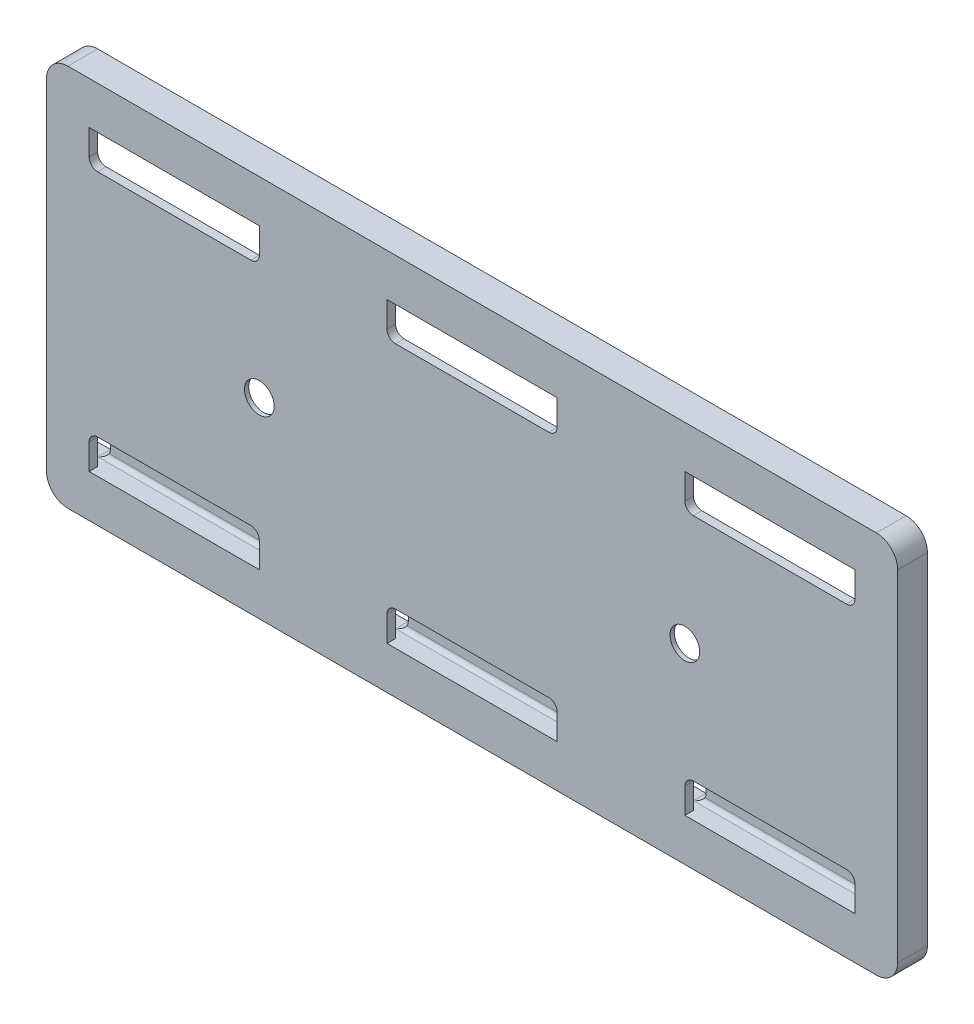
SolidWorks part; units mm, degrees
ref_plane "Plano frontal" through (0, 0, 0) normal (0, 0, 1) x (1, 0, 0)
ref_plane "Plano superior" through (0, 0, 0) normal (0, 1, 0) x (1, 0, 0)
ref_plane "Plano direito" through (0, 0, 0) normal (1, 0, 0) x (0, 0, -1)
sketch "Esboço1" plane through (0, 0, 0) normal (0, 0, 1) x (1, 0, 0)
  line L1 (-50, -22.5) -> (50, -22.5)
  line L2 (-50, -22.5) -> (-50, 22.5)
  line L3 (-50, 22.5) -> (50, 22.5)
  line L4 (50, -22.5) -> (50, 22.5)
  line L5 (-50, -22.5) -> (50, 22.5) construction
  line L6 (-50, 22.5) -> (50, -22.5) construction
  point P0 (0, 0)
  dimension "D1" = 45
  dimension "D2" = 100
extrude "Ressalto-extrusão1" add sketch "Esboço1" along normal blind 3.5
sketch "Esboço2" plane through (0, 0, 0) normal (0, 0, -1) x (-1, 0, 0)
  line L0 (-51.8558, 0) -> (52.4553, 0) construction
  line L1 (0.2997, 26.0278) -> (0.2997, -25.3284) construction
  line L2 (50, 22.5) -> (50, -22.5) construction
  line L3 (50, 17.5) -> (-47.5, 17.5)
  line L4 (50, 17.5) -> (50, -17.5)
  line L5 (50, -17.5) -> (-47.5, -17.5)
  line L6 (-47.5, 17.5) -> (-47.5, -17.5)
  line L7 (50, -22.5) -> (-50, -22.5) construction
  line L8 (-50, -22.5) -> (-50, 22.5) construction
  dimension "D1" = 35
  dimension "D2" = 5
  dimension "D3" = 2.5
extrude "Corte-extrusão1" cut sketch "Esboço2" against normal blind 2.5
sketch "Esboço4" plane through (0, 0, 0) normal (0, 0, -1) x (-1, 0, 0)
  line L0 (50, -22.5) -> (-50, -22.5) construction
  line L1 (-45, -22.5) -> (-25, -22.5)
  line L2 (-45, -22.5) -> (-45, -15.5)
  line L3 (-44, -14.5) -> (-26, -14.5)
  line L4 (-25, -22.5) -> (-25, -15.5)
  line L5 (50, -17.5) -> (50, 17.5) construction
  line L6 (-47.5, 17.5) -> (-47.5, -17.5) construction
  line L7 (0, 0) -> (-58.2504, 0) construction
  line L8 (-47.5, -17.5) -> (50, -17.5) construction
  line L10 (-10, -22.5) -> (10, -22.5)
  line L11 (-10, -22.5) -> (-10, -15.5)
  line L12 (-9, -14.5) -> (9, -14.5)
  line L13 (10, -22.5) -> (10, -15.5)
  line L14 (25, -22.5) -> (45, -22.5)
  line L15 (25, -22.5) -> (25, -15.5)
  line L16 (26, -14.5) -> (44, -14.5)
  line L17 (45, -22.5) -> (45, -15.5)
  line L19 (26, 14.5) -> (44, 14.5)
  line L20 (45, 22.5) -> (45, 15.5)
  line L21 (25, 22.5) -> (45, 22.5)
  line L22 (25, 22.5) -> (25, 15.5)
  line L23 (-9, 14.5) -> (9, 14.5)
  line L24 (10, 22.5) -> (10, 15.5)
  line L25 (-10, 22.5) -> (10, 22.5)
  line L26 (-10, 22.5) -> (-10, 15.5)
  line L27 (-44, 14.5) -> (-26, 14.5)
  line L28 (-25, 22.5) -> (-25, 15.5)
  line L29 (-45, 22.5) -> (-25, 22.5)
  line L30 (-45, 22.5) -> (-45, 15.5)
  arc A0 (-45, -15.5) -> (-44, -14.5) centre (-44, -15.5) cw
  arc A1 (-26, -14.5) -> (-25, -15.5) centre (-26, -15.5) cw
  arc A2 (-10, -15.5) -> (-9, -14.5) centre (-9, -15.5) cw
  arc A3 (9, -14.5) -> (10, -15.5) centre (9, -15.5) cw
  arc A4 (44, -14.5) -> (45, -15.5) centre (44, -15.5) cw
  arc A5 (25, -15.5) -> (26, -14.5) centre (26, -15.5) cw
  arc A6 (-44, 14.5) -> (-45, 15.5) centre (-44, 15.5) cw
  arc A7 (-26, 14.5) -> (-25, 15.5) centre (-26, 15.5) ccw
  arc A8 (-9, 14.5) -> (-10, 15.5) centre (-9, 15.5) cw
  arc A9 (9, 14.5) -> (10, 15.5) centre (9, 15.5) ccw
  arc A10 (26, 14.5) -> (25, 15.5) centre (26, 15.5) cw
  arc A11 (44, 14.5) -> (45, 15.5) centre (44, 15.5) ccw
  point P37 (-45, -14.5)
  point P40 (-25, -14.5)
  point P43 (-10, -14.5)
  point P46 (10, -14.5)
  point P49 (45, -14.5)
  point P52 (25, -14.5)
  point P55 (-45, 14.5)
  point P58 (-25, 14.5)
  point P61 (-10, 14.5)
  point P64 (10, 14.5)
  point P67 (25, 14.5)
  point P70 (45, 14.5)
  dimension "D10" = 1
  dimension "D11" = 1
  dimension "D12" = 1
  dimension "D13" = 1
  dimension "D14" = 1
  dimension "D15" = 1
  dimension "D16" = 1
  dimension "D17" = 1
  dimension "D18" = 1
  dimension "D19" = 1
  dimension "D20" = 1
  dimension "D1" = 20
  dimension "D2" = 8
  dimension "D3" = 2.5
  dimension "D4" = 20
  dimension "D5" = 20
  dimension "D6" = 5
  dimension "D7" = 8
  dimension "D8" = 8
  dimension "D9" = 15
extrude "Ressalto-extrusão2" add sketch "Esboço4" against normal blind 1
ref_plane "Plano1" through (0, 0, 3.5) normal (0, 0, 1) x (1, 0, 0)
sketch "Esboço5" plane through (0, 0, 3.5) normal (0, 0, 1) x (1, 0, 0)
  line L0 (0, 27.6414) -> (0, -29.0702) construction
  line L1 (57.481, 0) -> (-60.6683, 0) construction
  circle A0 centre (25, 0) radius 1.75
  circle A1 centre (-25, 0) radius 1.75
  dimension "D1" = 3.5
  dimension "D2" = 25
extrude "Corte-extrusão2" cut sketch "Esboço5" against normal blind 1.5
sketch "Esboço6" plane through (0, 0, 0) normal (0, 0, 1) x (1, 0, 0)
  line L1 (46.5, -18.5) -> (23.5, -18.5)
  line L2 (47.5, -19.5) -> (47.5, -20.5)
  line L3 (46.5, -21.5) -> (23.5, -21.5)
  line L4 (22.5, -19.5) -> (22.5, -20.5)
  line L5 (20.5, -18.5) -> (-21.5, -18.5)
  line L6 (21.5, -19.5) -> (21.5, -20.5)
  line L7 (20.5, -21.5) -> (-21.5, -21.5)
  line L8 (-22.5, -19.5) -> (-22.5, -20.5)
  line L9 (-24.5, -18.5) -> (-47.5, -18.5)
  line L10 (-23.5, -19.5) -> (-23.5, -20.5)
  line L11 (-24.5, -21.5) -> (-47.5, -21.5)
  line L12 (-48.5, -19.5) -> (-48.5, -20.5)
  line L13 (-50, -22.5) -> (50, -22.5) construction
  line L14 (47.5, 17.5) -> (47.5, -17.5) construction
  line L15 (-50, -17.5) -> (-50, -22.5) construction
  line L16 (57.4926, 0) -> (-59.95, 0) construction
  line L17 (-24.5, 21.5) -> (-47.5, 21.5)
  line L18 (-48.5, 19.5) -> (-48.5, 20.5)
  line L19 (-24.5, 18.5) -> (-47.5, 18.5)
  line L20 (-23.5, 19.5) -> (-23.5, 20.5)
  line L21 (20.5, 21.5) -> (-21.5, 21.5)
  line L22 (-22.5, 19.5) -> (-22.5, 20.5)
  line L23 (20.5, 18.5) -> (-21.5, 18.5)
  line L24 (21.5, 19.5) -> (21.5, 20.5)
  line L25 (46.5, 21.5) -> (23.5, 21.5)
  line L26 (22.5, 19.5) -> (22.5, 20.5)
  line L27 (46.5, 18.5) -> (23.5, 18.5)
  line L28 (47.5, 19.5) -> (47.5, 20.5)
  arc A0 (23.5, -21.5) -> (22.5, -20.5) centre (23.5, -20.5) cw
  arc A1 (23.5, -18.5) -> (22.5, -19.5) centre (23.5, -19.5) ccw
  arc A2 (47.5, -20.5) -> (46.5, -21.5) centre (46.5, -20.5) cw
  arc A3 (46.5, -18.5) -> (47.5, -19.5) centre (46.5, -19.5) cw
  arc A4 (-21.5, -21.5) -> (-22.5, -20.5) centre (-21.5, -20.5) cw
  arc A5 (-21.5, -18.5) -> (-22.5, -19.5) centre (-21.5, -19.5) ccw
  arc A6 (21.5, -20.5) -> (20.5, -21.5) centre (20.5, -20.5) cw
  arc A7 (20.5, -18.5) -> (21.5, -19.5) centre (20.5, -19.5) cw
  arc A8 (-47.5, -21.5) -> (-48.5, -20.5) centre (-47.5, -20.5) cw
  arc A9 (-47.5, -18.5) -> (-48.5, -19.5) centre (-47.5, -19.5) ccw
  arc A10 (-23.5, -20.5) -> (-24.5, -21.5) centre (-24.5, -20.5) cw
  arc A11 (-24.5, -18.5) -> (-23.5, -19.5) centre (-24.5, -19.5) cw
  arc A12 (-47.5, 21.5) -> (-48.5, 20.5) centre (-47.5, 20.5) ccw
  arc A13 (-47.5, 18.5) -> (-48.5, 19.5) centre (-47.5, 19.5) cw
  arc A14 (-23.5, 20.5) -> (-24.5, 21.5) centre (-24.5, 20.5) ccw
  arc A15 (-24.5, 18.5) -> (-23.5, 19.5) centre (-24.5, 19.5) ccw
  arc A16 (-21.5, 21.5) -> (-22.5, 20.5) centre (-21.5, 20.5) ccw
  arc A17 (-21.5, 18.5) -> (-22.5, 19.5) centre (-21.5, 19.5) cw
  arc A18 (21.5, 20.5) -> (20.5, 21.5) centre (20.5, 20.5) ccw
  arc A19 (20.5, 18.5) -> (21.5, 19.5) centre (20.5, 19.5) ccw
  arc A20 (23.5, 21.5) -> (22.5, 20.5) centre (23.5, 20.5) ccw
  arc A21 (23.5, 18.5) -> (22.5, 19.5) centre (23.5, 19.5) cw
  arc A22 (47.5, 20.5) -> (46.5, 21.5) centre (46.5, 20.5) ccw
  arc A23 (46.5, 18.5) -> (47.5, 19.5) centre (46.5, 19.5) ccw
  point P18 (22.5, -20)
  point P21 (22.5, -21.5)
  point P26 (47.5, -21.5)
  point P29 (47.5, -18.5)
  point P32 (-22.5, -21.5)
  point P37 (21.5, -21.5)
  point P40 (21.5, -18.5)
  point P43 (-48.5, -21.5)
  point P48 (-23.5, -21.5)
  point P51 (-23.5, -18.5)
  point P54 (-1.2287, 0)
  dimension "D10" = 1
  dimension "D13" = 1
  dimension "D14" = 1
  dimension "D1" = 3
  dimension "D2" = 1
  dimension "D3" = 3
  dimension "D4" = 3
  dimension "D5" = 1.5
  dimension "D6" = 25
  dimension "D7" = 25
  dimension "D8" = 44
  dimension "D9" = 1
  dimension "D11" = 1
  dimension "D12" = 1
extrude "Corte-extrusão4" cut sketch "Esboço6" along normal blind 2.5 contours L25 A20 L26 A21 L27 A23 L28 A22 | L21 A16 L22 A17 L23 A19 L24 A18 | L17 A12 L18 A13 L19 A15 L20 A14 | A11 L9 A9 L12 A8 L11 A10 L10 | L6 A6 L7 A4 L8 A5 L5 A7 | L2 A2 L3 A0 L4 A1 L1 A3
sketch "Esboço7" plane through (0, 0, 2.5) normal (0, 0, -1) x (-1, 0, 0)
  circle A0 centre (-25, 0) radius 3.5
  circle A1 centre (25, 0) radius 3.5
  dimension "D1" = 7
extrude "Corte-extrusão6" cut sketch "Esboço7" against normal blind 0.5
sketch "Esboço8" plane through (0, 0, 2.5) normal (0, 0, -1) x (-1, 0, 0)
  line L0 (-47.5, 17.5) -> (-47.5, -17.5) construction
  line L1 (-47.5, -7.5) -> (-46.2996, -7.5)
  line L2 (-47.5, -7.5) -> (-47.5, -12.5)
  line L3 (-47.5, -12.5) -> (-46.2996, -12.5)
  line L4 (-46.2996, -7.5) -> (-46.2996, -12.5)
  line L5 (-47.5, -17.5) -> (-45, -17.5) construction
  line L6 (-47.5, 2.5) -> (-46.5, 2.5)
  line L7 (-47.5, 2.5) -> (-47.5, -2.5)
  line L8 (-47.5, -2.5) -> (-46.5, -2.5)
  line L9 (-46.5, 2.5) -> (-46.5, -2.5)
  line L10 (-47.5, 12.5) -> (-46.5, 12.5)
  line L11 (-47.5, 12.5) -> (-47.5, 7.5)
  line L12 (-47.5, 7.5) -> (-46.5, 7.5)
  line L13 (-46.5, 12.5) -> (-46.5, 7.5)
  line L14 (50, 17.5) -> (-47.5, 17.5) construction
  dimension "D1" = 5
  dimension "D2" = 5
  dimension "D3" = 5
  dimension "D4" = 5
  dimension "D5" = 5
  dimension "D6" = 5
  dimension "D7" = 1
extrude "Ressalto-extrusão3" add sketch "Esboço8" along normal blind 1
fillet "Filete1" radius 2.5 1 edges at (-50, -22.5, 1.75)
fillet "Filete2" radius 2.5 1 edges at (50, -22.5, 1.75)
fillet "Filete3" radius 2.5 1 edges at (50, 22.5, 1.75)
fillet "Filete4" radius 2.5 1 edges at (-50, 22.5, 1.75)
fillet "Filete5" radius 0.5 1 edges at (46.2996, -12.5, 2)
fillet "Filete6" radius 0.5 1 edges at (46.2996, -7.5, 2)
fillet "Filete7" radius 0.5 1 edges at (46.5, -2.5, 2)
fillet "Filete8" radius 0.5 1 edges at (46.5, 2.5, 2)
fillet "Filete9" radius 0.5 1 edges at (46.5, 7.5, 2)
fillet "Filete10" radius 0.5 1 edges at (46.5, 12.5, 2)
fillet "Filete11" radius 1 1 edges at (45, 17.5, 0.5)
fillet "Filete12" radius 1 1 edges at (47.5, 17.5, 1.25)
fillet "Filete13" radius 1 1 edges at (25, 17.5, 0.5)
fillet "Filete14" radius 1 1 edges at (10, 17.5, 0.5)
fillet "Filete15" radius 1 1 edges at (-10, 17.5, 0.5)
fillet "Filete16" radius 1 1 edges at (-25, 17.5, 0.5)
fillet "Filete17" radius 1 1 edges at (-45, 17.5, 0.5)
fillet "Filete18" radius 0.5 1 edges at (-50, 17.5, 1.25)
fillet "Filete19" radius 0.5 1 edges at (-50, -17.5, 1.25)
fillet "Filete20" radius 1 1 edges at (-45, -17.5, 0.5)
fillet "Filete21" radius 1 1 edges at (-25, -17.5, 0.5)
fillet "Filete22" radius 1 1 edges at (-10, -17.5, 0.5)
fillet "Filete23" radius 1 1 edges at (10, -17.5, 0.5)
fillet "Filete24" radius 1 1 edges at (25, -17.5, 0.5)
fillet "Filete25" radius 1 1 edges at (45, -17.5, 0.5)
fillet "Filete26" radius 1 1 edges at (47.5, -17.5, 1.25)
fillet "Filete27" radius 0.5 1 edges at (35, -17.5, 1)
fillet "Filete28" radius 0.5 1 edges at (0, -17.5, 1)
fillet "Filete29" radius 0.5 1 edges at (-35, -17.5, 1)
fillet "Filete30" radius 0.5 1 edges at (-35, 17.5, 1)
fillet "Filete31" radius 0.5 1 edges at (0, 17.5, 1)
fillet "Filete32" radius 0.5 1 edges at (35, 17.5, 1)
sketch "Esboço9" plane through (0, 0, 2.5) normal (0, 0, -1) x (-1, 0, 0)
  line L0 (25, 16.5) -> (25, 15.5) construction
  line L1 (-45, 17.5) -> (-24.9988, 17.5)
  line L2 (-45, 17.5) -> (-45, 14.5)
  line L3 (-44, 13.5) -> (-25.9988, 13.5)
  line L4 (-24.9988, 17.5) -> (-24.9988, 14.5)
  line L5 (-10, 17.5) -> (10, 17.5)
  line L6 (-47.5, 16.5) -> (-47.5, 12.5) construction
  line L7 (-47.5, 22.5) -> (47.5, 22.5) construction
  line L8 (-10, 17.5) -> (-10, 14.5)
  line L9 (-9, 13.5) -> (9, 13.5)
  line L10 (10, 17.5) -> (10, 14.5)
  line L11 (25, 17.5) -> (45, 17.5)
  line L12 (25, 17.5) -> (25, 14.5)
  line L13 (26, 13.5) -> (44, 13.5)
  line L14 (45, 17.5) -> (45, 14.5)
  line L15 (0, 0) -> (-3.3797, 0) construction
  line L16 (26, -13.5) -> (44, -13.5)
  line L17 (45, -17.5) -> (45, -14.5)
  line L18 (25, -17.5) -> (45, -17.5)
  line L19 (25, -17.5) -> (25, -14.5)
  line L20 (-9, -13.5) -> (9, -13.5)
  line L21 (10, -17.5) -> (10, -14.5)
  line L22 (-10, -17.5) -> (10, -17.5)
  line L23 (-10, -17.5) -> (-10, -14.5)
  line L24 (-44, -13.5) -> (-25.9988, -13.5)
  line L25 (-24.9988, -17.5) -> (-24.9988, -14.5)
  line L26 (-45, -17.5) -> (-24.9988, -17.5)
  line L27 (-45, -17.5) -> (-45, -14.5)
  arc A0 (44, 13.5) -> (45, 14.5) centre (44, 14.5) ccw
  arc A1 (25, 14.5) -> (26, 13.5) centre (26, 14.5) ccw
  arc A2 (9, 13.5) -> (10, 14.5) centre (9, 14.5) ccw
  arc A3 (-10, 14.5) -> (-9, 13.5) centre (-9, 14.5) ccw
  arc A4 (-25.9988, 13.5) -> (-24.9988, 14.5) centre (-25.9988, 14.5) ccw
  arc A5 (-45, 14.5) -> (-44, 13.5) centre (-44, 14.5) ccw
  arc A6 (44, -13.5) -> (45, -14.5) centre (44, -14.5) cw
  arc A7 (25, -14.5) -> (26, -13.5) centre (26, -14.5) cw
  arc A8 (9, -13.5) -> (10, -14.5) centre (9, -14.5) cw
  arc A9 (-10, -14.5) -> (-9, -13.5) centre (-9, -14.5) cw
  arc A10 (-25.9988, -13.5) -> (-24.9988, -14.5) centre (-25.9988, -14.5) cw
  arc A11 (-45, -14.5) -> (-44, -13.5) centre (-44, -14.5) cw
  point P20 (45, 13.5)
  point P23 (25, 13.5)
  point P26 (10, 13.5)
  point P29 (-10, 13.5)
  point P34 (-45, 13.5)
  dimension "D7" = 1
  dimension "D1" = 2.5
  dimension "D2" = 5
  dimension "D3" = 4
  dimension "D4" = 20
  dimension "D5" = 20
  dimension "D6" = 4
extrude "Corte-extrusão7" cut sketch "Esboço9" against normal blind 1
fillet "Filete33" radius 0.5 1 edges at (47.5, -10, 1.5)
fillet "Filete34" radius 0.5 3 edges at (47.5, 0, 1.5) (47.25, -2.5, 1.5) (47.25, 2.5, 1.5)
fillet "Filete35" radius 0.5 3 edges at (47.5, 10, 1.5) (47.25, 7.5, 1.5) (47.25, 12.5, 1.5)
sketch "Esboço10" plane through (0, 0, 0) normal (0, 0, -1) x (-1, 0, 0)
  line L0 (-10, 17.5) -> (-10, 14.5) construction
  line L1 (-45, 16.5) -> (-24.9988, 16.5)
  line L2 (-45, 16.5) -> (-45, 14.5)
  line L3 (-45, 14.5) -> (-24.9988, 14.5)
  line L4 (-24.9988, 16.5) -> (-24.9988, 14.5)
  line L5 (-10, 16.5) -> (10, 16.5)
  line L6 (-10, 16.5) -> (-10, 14.5)
  line L7 (-10, 14.5) -> (10, 14.5)
  line L8 (10, 16.5) -> (10, 14.5)
  line L9 (0, 0) -> (-12.9211, 0) construction
  line L10 (45, 16.5) -> (25, 16.5)
  line L11 (45, 16.5) -> (45, 14.5)
  line L12 (45, 14.5) -> (25, 14.5)
  line L13 (25, 16.5) -> (25, 14.5)
  line L14 (45, -14.5) -> (25, -14.5)
  line L15 (25, -16.5) -> (25, -14.5)
  line L16 (45, -16.5) -> (25, -16.5)
  line L17 (45, -16.5) -> (45, -14.5)
  line L18 (-10, -14.5) -> (10, -14.5)
  line L19 (10, -16.5) -> (10, -14.5)
  line L20 (-10, -16.5) -> (10, -16.5)
  line L21 (-10, -16.5) -> (-10, -14.5)
  line L22 (-45, -14.5) -> (-24.9988, -14.5)
  line L23 (-24.9988, -16.5) -> (-24.9988, -14.5)
  line L24 (-45, -16.5) -> (-24.9988, -16.5)
  line L25 (-45, -16.5) -> (-45, -14.5)
  arc A0 (-10, 16.5) -> (-11, 17.5) centre (-11, 16.5) ccw construction
extrude "Ressalto-extrusão4" add sketch "Esboço10" against normal blind 1
fillet "Filete36" radius 0.5 1 edges at (-35, 14.5, 1)
fillet "Filete37" radius 0.5 1 edges at (0, 14.5, 1)
fillet "Filete38" radius 0.5 1 edges at (34.9994, 14.5, 1)
fillet "Filete39" radius 0.5 1 edges at (-35, -14.5, 1)
fillet "Filete40" radius 0.5 1 edges at (0, -14.5, 1)
fillet "Filete41" radius 0.5 1 edges at (34.9994, -14.5, 1)
sketch "Esboço11" plane through (0, 0, 0) normal (1, 0, 0) x (0, 0, -1)
  line L0 (0, 15) -> (-0.5, 15)
  line L1 (0, 14.5) -> (0, 16.5) construction
  line L6 (0, 15) -> (0, 14.3607)
  line L8 (0, 16.5) -> (0, -16.5) construction
  line L10 (0, 14.3607) -> (-1.2301, 14.3607)
  line L13 (-0.5, 14.5) -> (0, 14.5) construction
  line L16 (-1.2301, 15) -> (-1.2301, 14.3607)
  line L17 (-1.2301, 15) -> (-1.2301, 15.6752)
  line L18 (-1.2301, 15.6752) -> (-1, 15.6752)
  line L19 (-1, 15.6752) -> (-1, 15.5)
  line L20 (-1, 15) -> (-1, 16.5) construction
  line L21 (2.3481, 0) -> (-6.2369, 0) construction
  line L22 (-1.2301, -15) -> (-1.2301, -15.6752)
  line L23 (-1.2301, -15.6752) -> (-1, -15.6752)
  line L24 (-1, -15.6752) -> (-1, -15.5)
  line L25 (0, -15) -> (-0.5, -15)
  line L26 (0, -15) -> (0, -14.3607)
  line L27 (0, -14.3607) -> (-1.2301, -14.3607)
  line L28 (-1.2301, -15) -> (-1.2301, -14.3607)
  arc A0 (-0.5, 15) -> (-1, 15.5) centre (-0.5, 15.5) cw
  arc A1 (-0.5, -15) -> (-1, -15.5) centre (-0.5, -15.5) ccw
  dimension "D1" = 0.5
  dimension "D2" = 0.5
extrude "Corte-extrusão8" cut sketch "Esboço11" against normal mid plane 91
